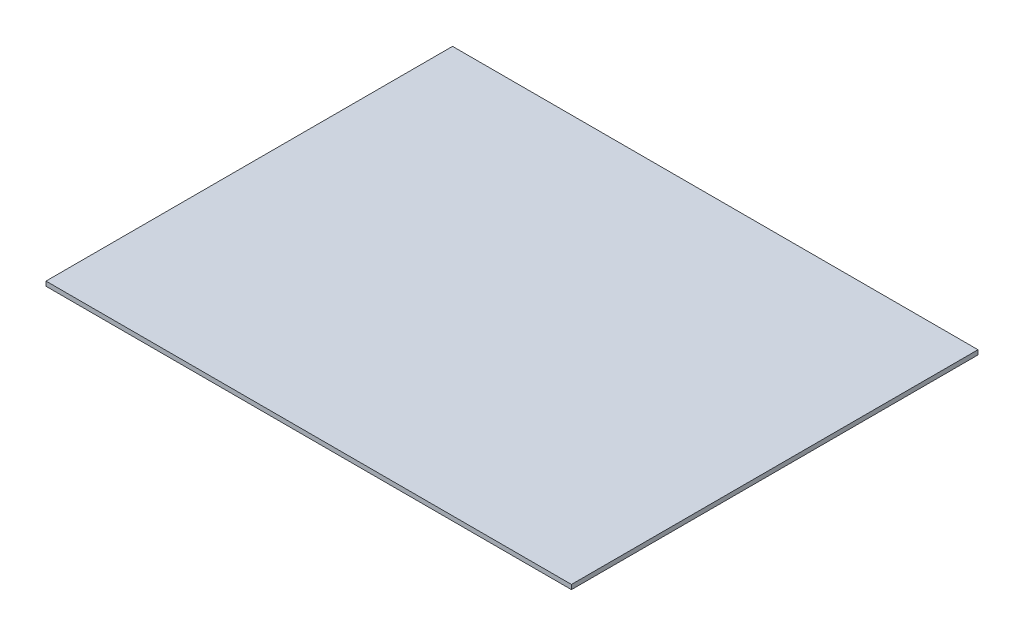
SolidWorks part; units mm, degrees
ref_plane "Спереди" through (0, 0, 0) normal (0, 0, 1) x (1, 0, 0)
ref_plane "Сверху" through (0, 0, 0) normal (0, 1, 0) x (1, 0, 0)
ref_plane "Справа" through (0, 0, 0) normal (1, 0, 0) x (0, 0, -1)
sketch "Эскиз1" plane through (0, 0, 0) normal (0, 1, 0) x (1, 0, 0)
  line L1 (-232, -179.5) -> (232, -179.5)
  line L2 (-232, -179.5) -> (-232, 179.5)
  line L3 (-232, 179.5) -> (232, 179.5)
  line L4 (232, -179.5) -> (232, 179.5)
  line L5 (-232, -179.5) -> (232, 179.5) construction
  line L6 (-232, 179.5) -> (232, -179.5) construction
  point P0 (0, 0)
  dimension "D1" = 359
  dimension "D2" = 464
extrude "Бобышка-Вытянуть1" add sketch "Эскиз1" along normal blind 4
